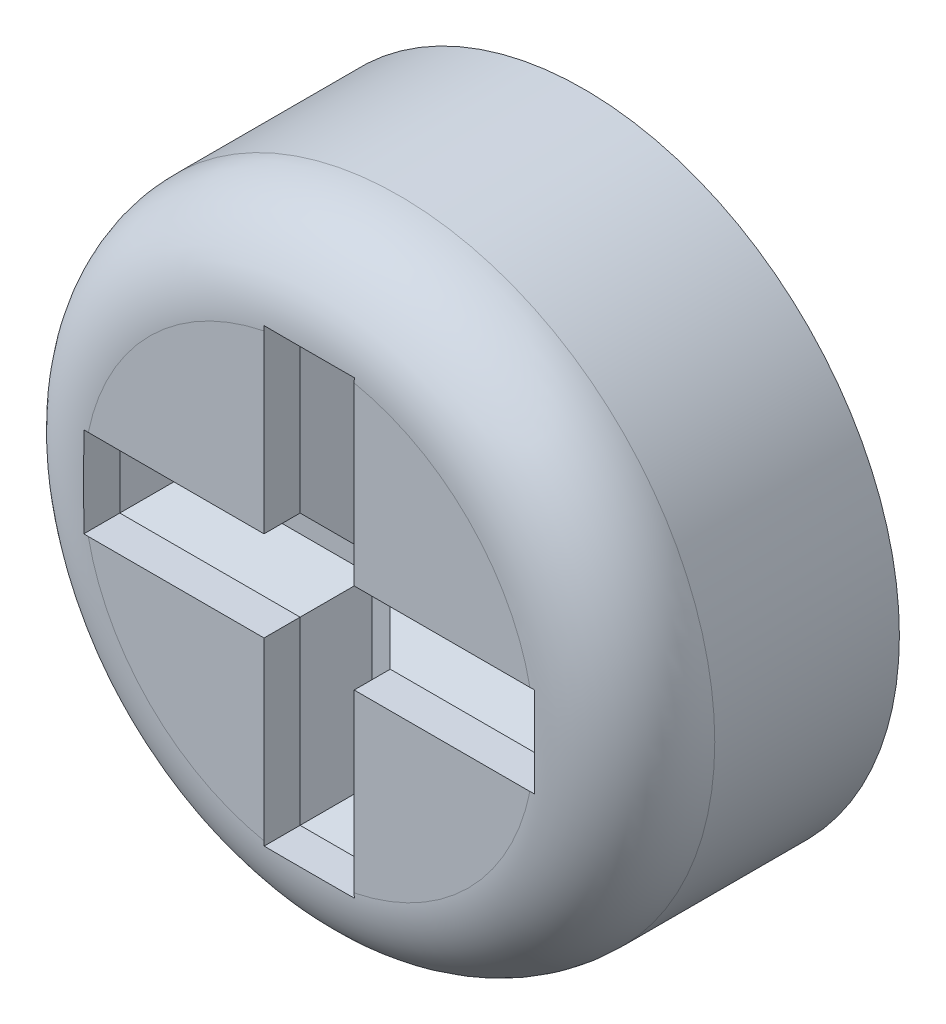
SolidWorks part; units mm, degrees
ref_plane "Front" through (0, 0, 0) normal (0, 0, 1) x (1, 0, 0)
ref_plane "Top" through (0, 0, 0) normal (0, 1, 0) x (1, 0, 0)
ref_plane "Right" through (0, 0, 0) normal (1, 0, 0) x (0, 0, -1)
sketch "Sketch1" plane through (0, 0, 0) normal (0, 0, 1) x (1, 0, 0)
  circle A0 centre (0, 0) radius 1.75
  dimension "D1" = 3.5
extrude "Extrude1" add sketch "Sketch1" along normal blind 1.524
fillet "Fillet1" radius 0.5
sketch "Sketch2" plane through (0, 0, 1.524) normal (0, 0, 1) x (1, 0, 0)
  line L0 (0.25, -0.25) -> (0.25, -1.25)
  line L1 (-0.25, 1.25) -> (0.25, 1.25)
  line L2 (-0.25, 1.25) -> (-0.25, 0.25)
  line L3 (-0.25, -1.25) -> (0.25, -1.25)
  line L4 (0.25, 1.25) -> (0.25, 0.25)
  line L5 (-1.25, 0.25) -> (-0.25, 0.25)
  line L6 (-1.25, 0.25) -> (-1.25, -0.25)
  line L7 (-1.25, -0.25) -> (-0.25, -0.25)
  line L8 (1.25, 0.25) -> (1.25, -0.25)
  line L9 (0.25, 0.25) -> (1.25, 0.25)
  line L10 (-0.25, -0.25) -> (-0.25, -1.25)
  line L11 (0.25, -0.25) -> (1.25, -0.25)
  dimension "D1" = 1.25
  dimension "D2" = 2.5
  dimension "D3" = 1.25
  dimension "D4" = 2.5
  dimension "D5" = 0.5
  dimension "D6" = 0.25
  dimension "D7" = 0.25
  dimension "D8" = 0.5
extrude "Cut-Extrude2" cut sketch "Sketch2" against normal blind 0.4
chamfer "Chamfer1" distance 0.2 angle 45
